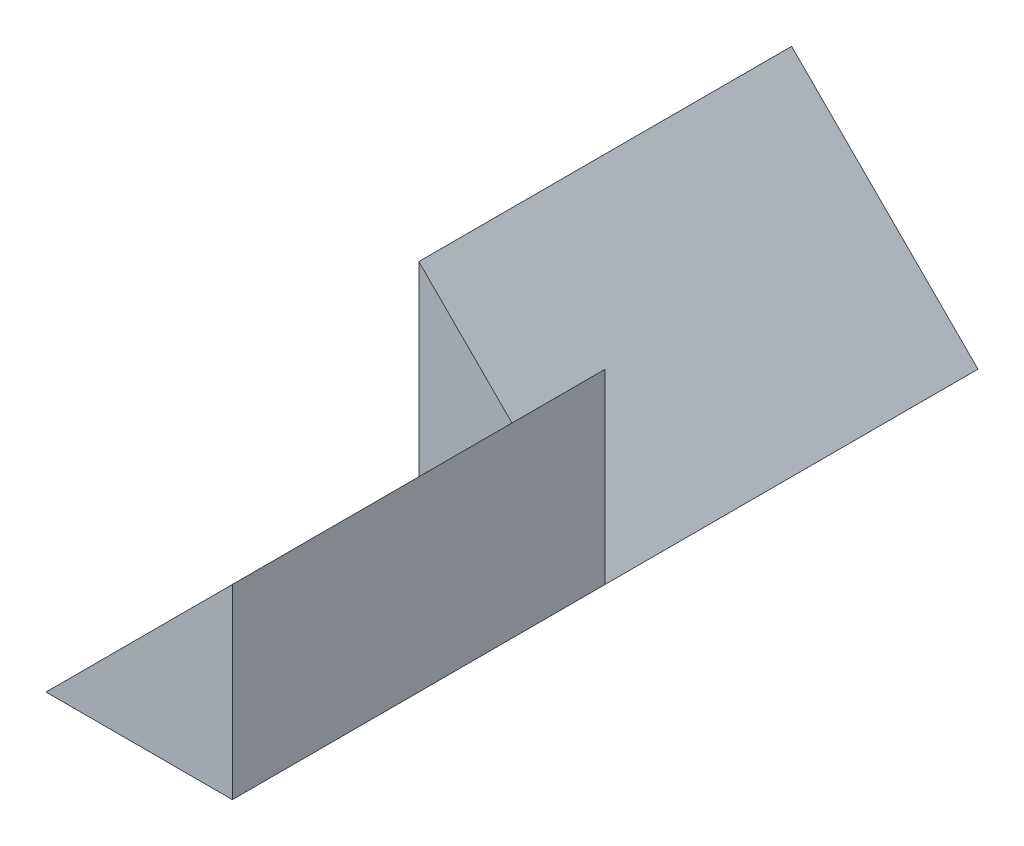
SolidWorks part; units mm, degrees
ref_plane "Front Plane" through (0, 0, 0) normal (0, 0, 1) x (1, 0, 0)
ref_plane "Top Plane" through (0, 0, 0) normal (0, 1, 0) x (1, 0, 0)
ref_plane "Right Plane" through (0, 0, 0) normal (1, 0, 0) x (0, 0, -1)
sketch "Sketch1" plane through (0, 0, 0) normal (0, 0, 1) x (1, 0, 0)
  line L0 (0, 0) -> (0, 1)
  line L1 (0, 1) -> (1, 0)
  line L2 (1, 0) -> (0, 0)
  dimension "D1" = 45
  dimension "D2" = 1
extrude "Boss-Extrude1" add sketch "Sketch1" along normal blind 2
sketch "Sketch2" plane through (0, 0, 2) normal (0, 0, 1) x (1, 0, 0)
  line L0 (1, 0) -> (1, 1)
  line L1 (1, 1) -> (0, 0)
  line L2 (0, 0) -> (1, 0)
  line L3 (0, 1) -> (1, 1) construction
extrude "Boss-Extrude2" add sketch "Sketch2" along normal blind 2
